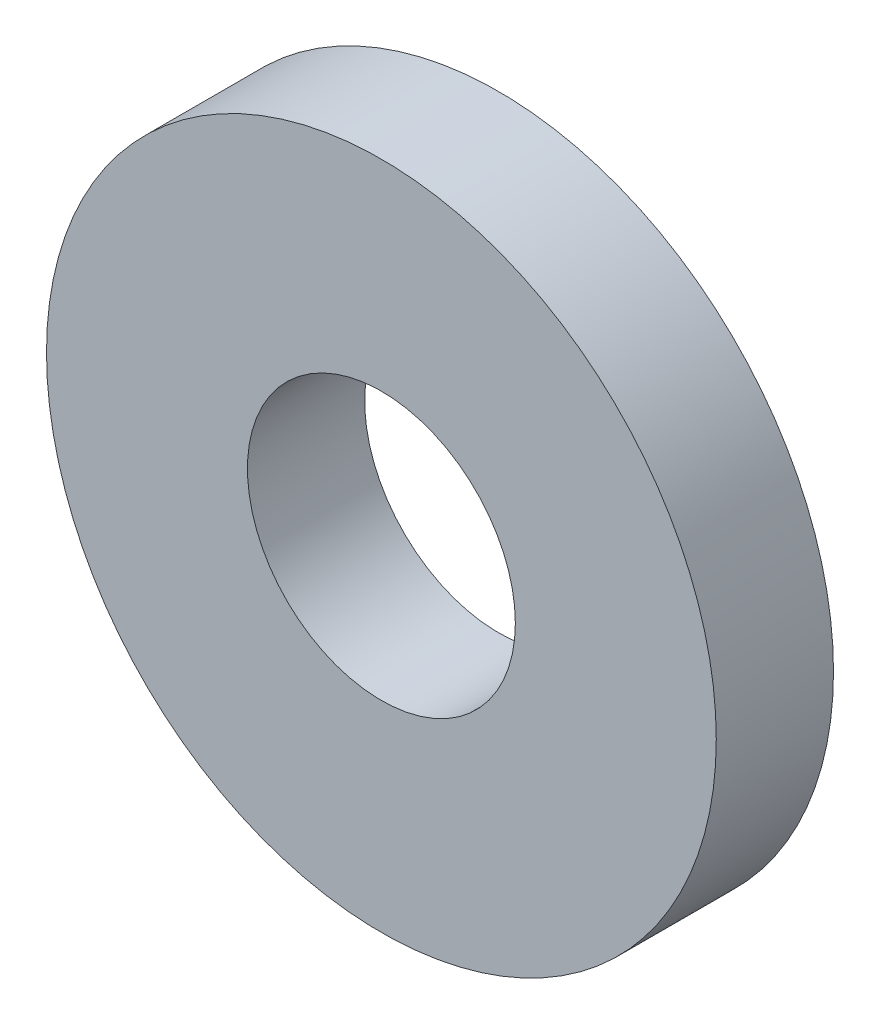
SolidWorks part; units mm, degrees
ref_plane "Спереди" through (0, 0, 0) normal (0, 0, 1) x (1, 0, 0)
ref_plane "Сверху" through (0, 0, 0) normal (0, 1, 0) x (1, 0, 0)
ref_plane "Справа" through (0, 0, 0) normal (1, 0, 0) x (0, 0, -1)
sketch "Эскиз1" plane through (0, 0, 0) normal (0, 0, 1) x (1, 0, 0)
  circle A0 centre (0, 0) radius 1.6
  circle A1 centre (0, 0) radius 4
  dimension "D1" = 3.2
  dimension "D2" = 8
extrude "Бобышка-Вытянуть1" add sketch "Эскиз1" along normal blind 1.4
